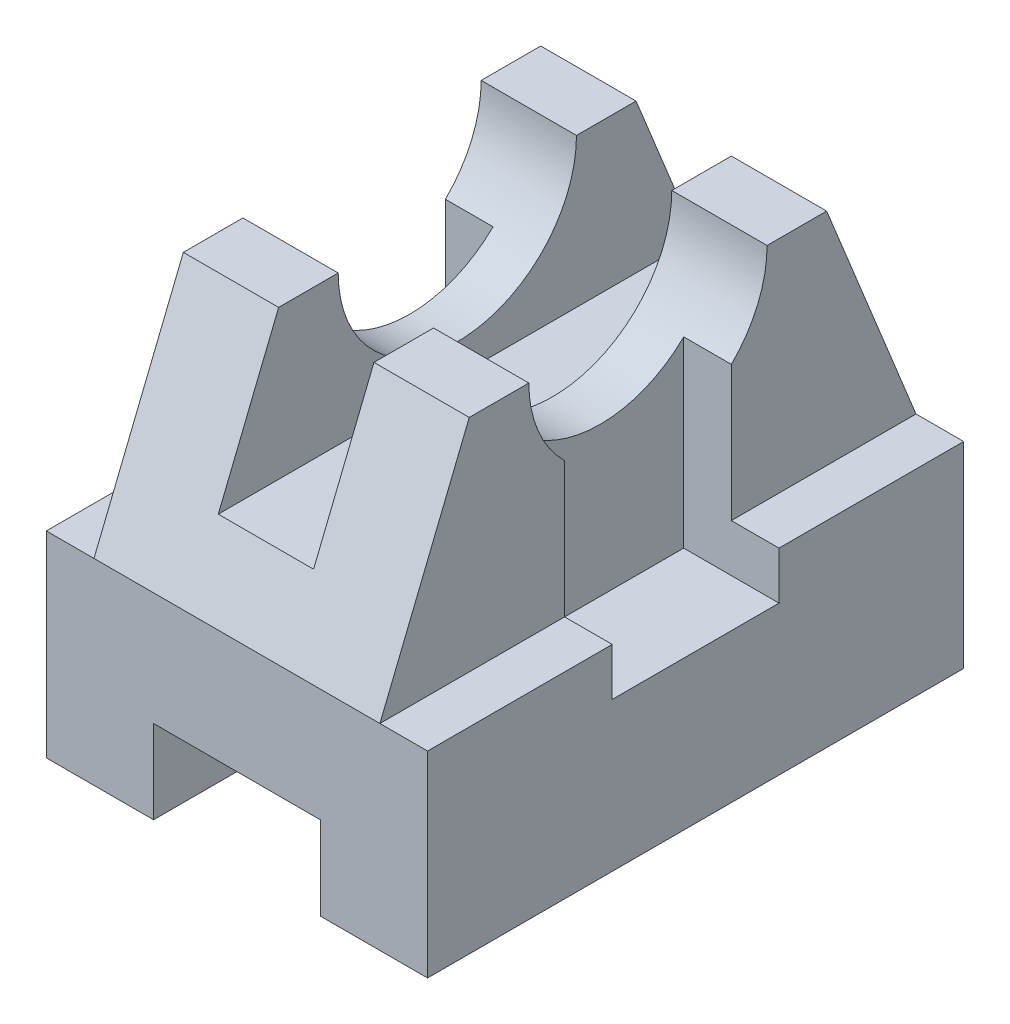
SolidWorks part; units mm, degrees
ref_plane "Front Plane" through (0, 0, 0) normal (0, 0, 1) x (1, 0, 0)
ref_plane "Top Plane" through (0, 0, 0) normal (0, 1, 0) x (1, 0, 0)
ref_plane "Right Plane" through (0, 0, 0) normal (1, 0, 0) x (0, 0, -1)
sketch "Sketch1" plane through (0, 0, 0) normal (0, 1, 0) x (1, 0, 0)
  line L1 (-32, 45) -> (32, 45)
  line L2 (-32, 45) -> (-32, -45)
  line L3 (-32, -45) -> (32, -45)
  line L4 (32, 45) -> (32, -45)
  line L5 (-32, 45) -> (32, -45) construction
  line L6 (-32, -45) -> (32, 45) construction
  point P0 (0, 0)
  dimension "D1" = 90
  dimension "D2" = 64
extrude "Boss-Extrude1" add sketch "Sketch1" along normal blind 33
sketch "Sketch2" plane through (0, 0, 0) normal (1, 0, 0) x (0, 0, -1)
  line L0 (45, 33) -> (-45, 33)
  line L1 (-45, 33) -> (-30, 70)
  line L2 (-30, 70) -> (-20, 70)
  line L3 (30, 70) -> (45, 33)
  line L4 (0, 70) -> (0, 33) construction
  line L5 (20, 70) -> (30, 70)
  arc A0 (-20, 70) -> (20, 70) centre (0, 70) ccw
  dimension "D3" = 40
  dimension "D1" = 60
  dimension "D2" = 37
extrude "Boss-Extrude2" add sketch "Sketch2" along normal mid plane 48
sketch "Sketch3" plane through (0, 70, 0) normal (0, 1, 0) x (1, 0, 0)
  line L1 (-8, 46.2602) -> (8, 46.2602)
  line L2 (-8, 46.2602) -> (-8, -46.2602)
  line L3 (-8, -46.2602) -> (8, -46.2602)
  line L4 (8, 46.2602) -> (8, -46.2602)
  line L5 (-8, 46.2602) -> (8, -46.2602) construction
  line L6 (-8, -46.2602) -> (8, 46.2602) construction
  point P0 (0, 0)
  dimension "D1" = 16
extrude "Cut-Extrude1" cut sketch "Sketch3" against normal blind 25
sketch "Sketch6" plane through (0, 70, 0) normal (0, 1, 0) x (1, 0, 0)
  line L0 (-32, 0) -> (32, 0) construction
  line L1 (-32, 45) -> (-32, -45) construction
  line L2 (32, -45) -> (32, 45) construction
  line L4 (32, 14) -> (16, 14)
  line L5 (32, 14) -> (32, -14)
  line L6 (32, -14) -> (16, -14)
  line L7 (16, 14) -> (16, -14)
  line L8 (-32, 14) -> (-16, 14)
  line L9 (-32, 14) -> (-32, -14)
  line L10 (-32, -14) -> (-16, -14)
  line L11 (-16, 14) -> (-16, -14)
  dimension "D1" = 28
  dimension "D2" = 16
  dimension "D3" = 14
extrude "Cut-Extrude3" cut sketch "Sketch6" against normal blind 45
sketch "Sketch7" plane through (0, 0, 45) normal (0, 0, 1) x (1, 0, 0)
  line L0 (-32, 0) -> (32, 0) construction
  line L1 (-14, 0) -> (14, 0)
  line L2 (-14, 0) -> (-14, 14)
  line L3 (-14, 14) -> (14, 14)
  line L4 (14, 0) -> (14, 14)
  point P6 (0, 14)
  dimension "D1" = 28
  dimension "D2" = 14
extrude "Cut-Extrude4" cut sketch "Sketch7" against normal through all
